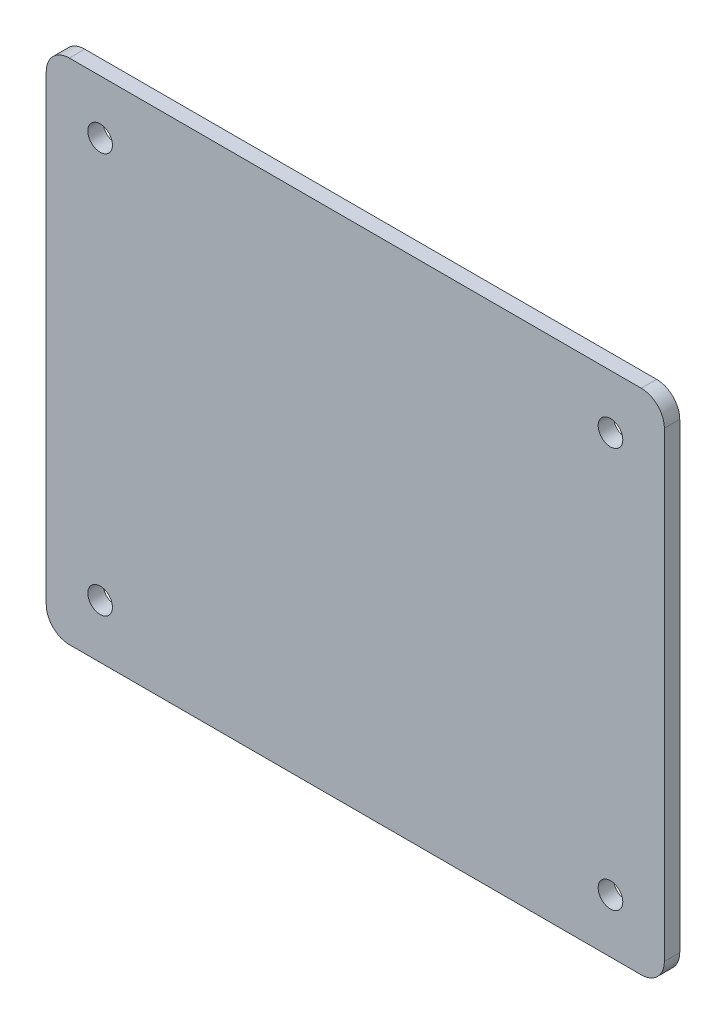
SolidWorks part; units mm, degrees
material "Acrylic (Medium-high impact)"
ref_plane "Front Plane" through (0, 0, 0) normal (0, 0, 1) x (1, 0, 0)
ref_plane "Top Plane" through (0, 0, 0) normal (0, 1, 0) x (1, 0, 0)
ref_plane "Right Plane" through (0, 0, 0) normal (1, 0, 0) x (0, 0, -1)
sketch "Sketch1" plane through (0, 0, 0) normal (0, 0, 1) x (1, 0, 0)
  line L1 (0, 0) -> (80.3, 0)
  line L2 (0, 0) -> (0, 66)
  line L3 (0, 66) -> (80.3, 66)
  line L4 (80.3, 0) -> (80.3, 66)
  dimension "D1" = 80.3
  dimension "D2" = 66
extrude "Boss-Extrude1" add sketch "Sketch1" along normal blind 2
hole_wizard "Ø3.2 (3.2) Diameter Hole1" positions "Sketch3" profile "Sketch2" hole size "Ø3.2" standard "ANSI Metric" end condition through all
sketch "Sketch3" plane through (0, 0, 2) normal (0, 0, 1) x (1, 0, 0)
  line L0 (0, 33) -> (80.3, 33) construction
  line L1 (0, 66) -> (0, 0) construction
  line L2 (80.3, 0) -> (80.3, 66) construction
  line L4 (7, 7) -> (7, 59) construction
  line L6 (7, 59) -> (73.3, 59) construction
  line L7 (73.3, 59) -> (73.3, 7) construction
  line L8 (73.3, 7) -> (7, 7) construction
  line L10 (40.15, 66) -> (40.15, 0) construction
  line L11 (80.3, 66) -> (0, 66) construction
  line L12 (0, 0) -> (80.3, 0) construction
  point P0 (7, 59)
  point P2 (73.3, 59)
  point P4 (73.3, 7)
  point P6 (7, 7)
  dimension "D1" = 66.3
  dimension "D2" = 52
  dimension "D3" = 26
  dimension "D4" = 33.15
sketch "Sketch2" plane through (7, 59, 2) normal (1, 0, 0) x (0, -1, 0)
  line L0 (0, 0) -> (0, 2)
  line L1 (0, 2) -> (1.6, 2)
  line L2 (1.6, 2) -> (1.6, 0)
  line L5 (1.6, 0) -> (0, 0)
  line L11 (0, -6.35) -> (0, 107.95) construction
  dimension "Thru Hole Dia." = 3.2
  dimension "Thru Hole Depth" = 2
fillet "Fillet1" radius 3 4 edges at (80.3, 66, 1) (80.3, 0, 1) (0, 0, 1) (0, 66, 1)
